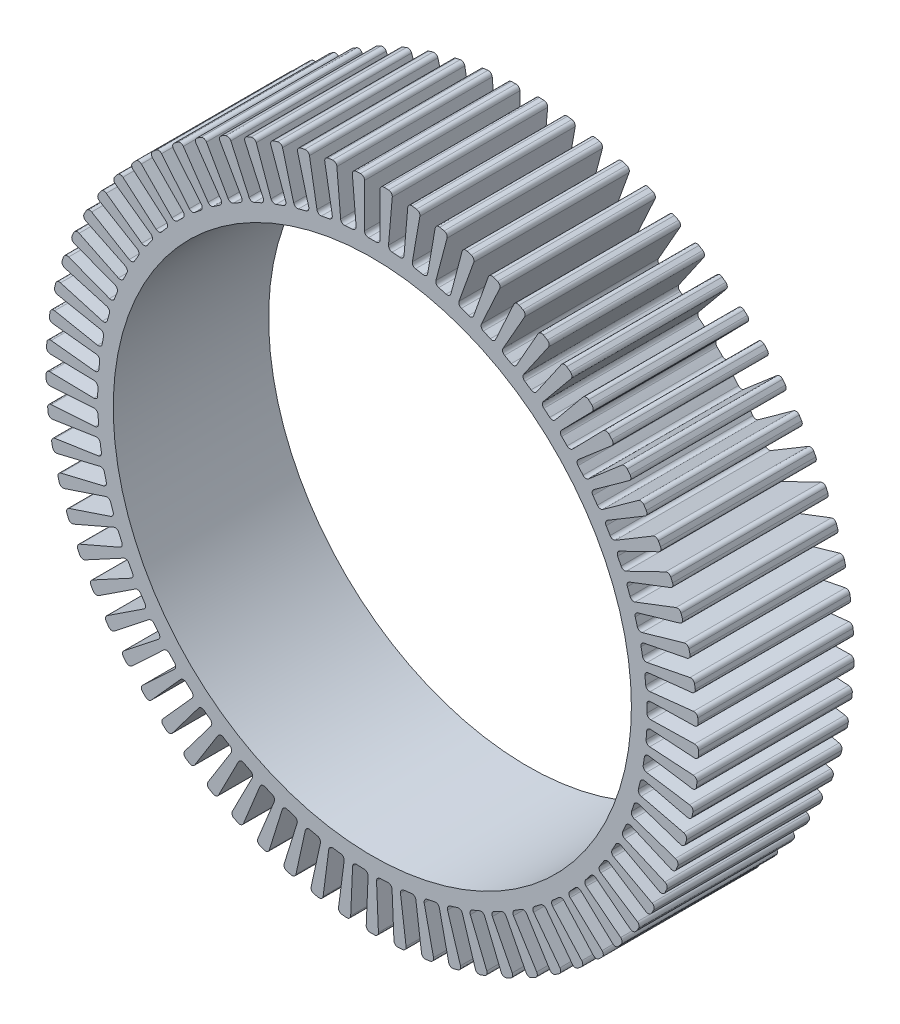
SolidWorks part; units mm, degrees
material "6061 合金"
ref_plane "前视基准面" through (0, 0, 0) normal (0, 0, 1) x (1, 0, 0)
ref_plane "上视基准面" through (0, 0, 0) normal (0, 1, 0) x (1, 0, 0)
ref_plane "右视基准面" through (0, 0, 0) normal (1, 0, 0) x (0, 0, -1)
sketch "草图1" plane through (0, 0, 0) normal (0, 0, 1) x (1, 0, 0)
  circle A0 centre (0, 0) radius 42
  circle A1 centre (0, 0) radius 33.35
  dimension "D1" = 66.7
  dimension "D2" = 84
extrude "凸台-拉伸1" add sketch "草图1" along normal mid plane 20
sketch "草图2" plane through (0, 0, 10) normal (0, 0, 1) x (1, 0, 0)
  line L0 (0, 42) -> (0, 0) construction
  line L1 (-1, 41.9881) -> (-1, 35.3359)
  line L2 (1, 41.9881) -> (1, 35.3359)
  circle A0 centre (0, 0) radius 42 construction
  arc A2 (1, 41.9881) -> (-1, 41.9881) centre (0, 0) ccw
  circle A6 centre (0, 0) radius 35.35
  arc A7 (1, 35.3359) -> (-1, 35.3359) centre (0, 0) ccw
  dimension "D1" = 2
  dimension "D2" = 2
extrude "切除-拉伸1" cut sketch "草图2" against normal blind 20
pattern_circular "阵列(圆周)1" count 73 over 360 about axis through (0, 0, 0) along (0, 0, 1) of "切除-拉伸1"
fillet "圆角1" radius 0.5 54 edges at (26.0598, -32.9376, 0) (27.3066, -31.9116, 0) (22.8625, -26.9616, 0) (28.3803, -21.0756, 0) (32.0261, -14.9651, 0) (34.1161, -9.2581, 0) (41.3626, -7.2892, 0) (41.6627, -5.3119, 0) (41.9999, -0.0963, 0) (35.3492, -0.2395, 0) (35.3062, 1.7601, 0) (41.9569, 1.9032, 0) (37.3371, 19.2338, 0) (36.5702, 20.6547, 0) (30.8575, 17.2463, 0) (25.4306, 24.5541, 0) (24.0013, 25.9531, 0) (22.9708, 35.1617, 0) (16.6083, 38.5767, 0) (10.9853, 33.5998, 0) (8.1775, 41.1962, 0) (2.0413, 35.291, 0) (1, 41.9881, 0) (-15.6507, 31.6967, 0) (-16.5784, 31.2215, 0) (-23.2257, 26.6494, 0) (-27.4527, 31.786, 0) (-24.0013, 25.9531, 0) (-25.4306, 24.5541, 0) (-35.5455, 22.3723, 0) (-29.8328, 18.9638, 0) (-33.3556, 11.7057, 0) (-39.5677, 14.0852, 0) (-33.6862, 10.7173, 0) (-34.4828, 7.7817, 0) (-41.6379, 5.503, 0) (-41.9569, 1.9032, 0) (-41.9999, -0.0963, 0) (-35.3268, -1.2815, 0) (-41.6627, -5.3119, 0) (-34.5851, -7.3138, 0) (-40.5829, -10.818, 0) (-39.5027, -14.2666, 0) (-36.4751, -20.8223, 0) (-35.6478, -22.2089, 0) (-26.4635, -23.4373, 0) (-17.9063, -30.4793, 0) (-16.9999, -30.994, 0) (-11.4396, -33.4479, 0) (-2.5193, -35.2601, 0) (0.8073, -41.9922, 0) (2.8055, -41.9062, 0) (11.5034, -40.3939, 0) (14.2726, -32.3406, 0)
